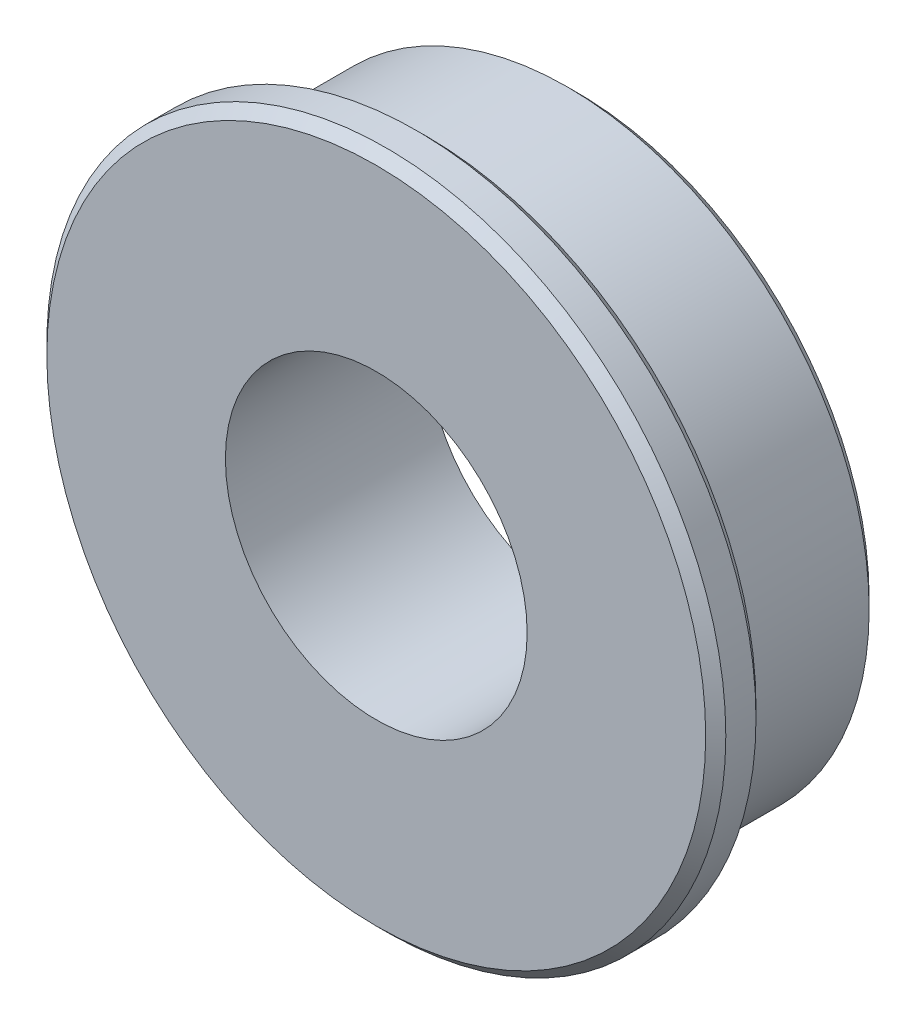
SolidWorks part; units mm, degrees
ref_plane "前视基准面" through (0, 0, 0) normal (0, 0, 1) x (1, 0, 0)
ref_plane "上视基准面" through (0, 0, 0) normal (0, 1, 0) x (1, 0, 0)
ref_plane "右视基准面" through (0, 0, 0) normal (1, 0, 0) x (0, 0, -1)
sketch "草图1" plane through (0, 0, 0) normal (0, 0, 1) x (1, 0, 0)
  circle A0 centre (0, 0) radius 6
  circle A1 centre (0, 0) radius 3
  dimension "D1" = 12
  dimension "D2" = 6
extrude "凸台-拉伸1" add sketch "草图1" along normal mid plane 4
sketch "草图2" plane through (0, 0, 2) normal (0, 0, 1) x (1, 0, 0)
  circle A0 centre (0, 0) radius 6.75
  circle A2 centre (0, 0) radius 3 construction
  circle A3 centre (0, 0) radius 3
  dimension "D1" = 13.5
extrude "凸台-拉伸2" add sketch "草图2" against normal blind 1
chamfer "倒角1" distance 0.2 angle 45 3 edges at (6, 0, -2) (6.75, 0, 1) (6.75, 0, 2)
